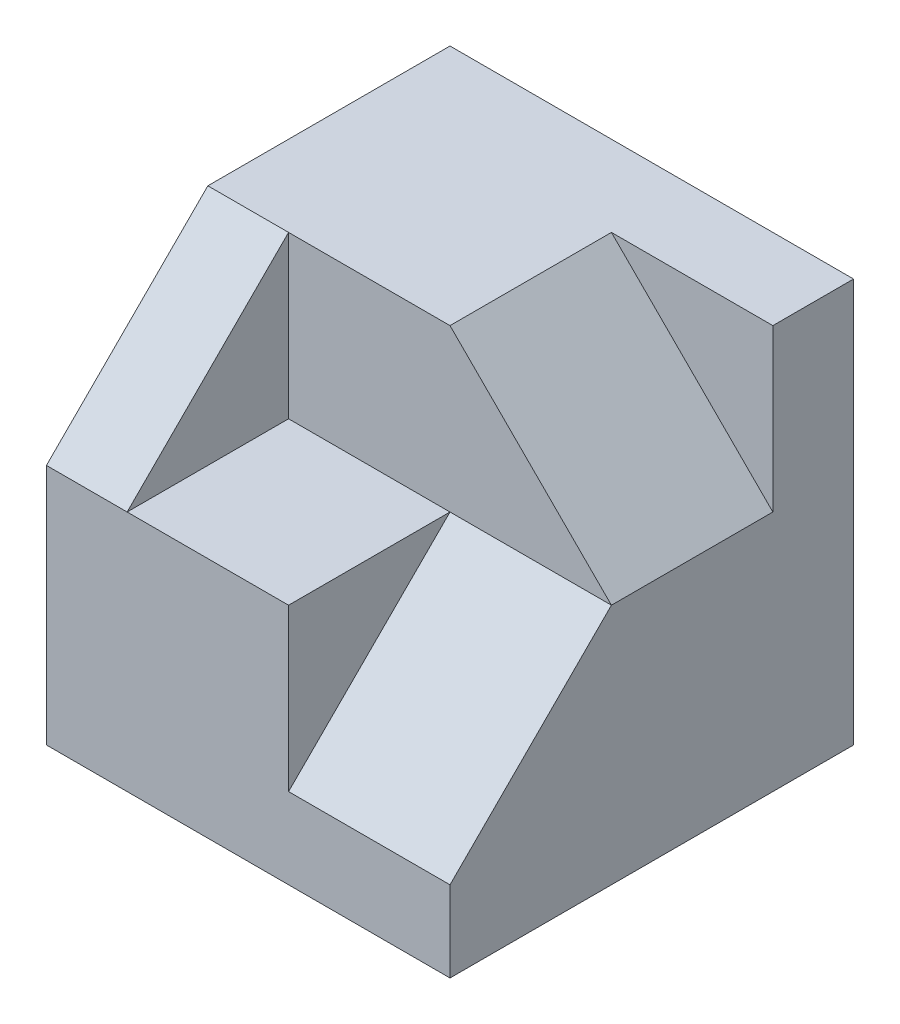
SolidWorks part; units mm, degrees
ref_plane "Front Plane" through (0, 0, 0) normal (0, 0, 1) x (1, 0, 0)
ref_plane "Top Plane" through (0, 0, 0) normal (0, 1, 0) x (1, 0, 0)
ref_plane "Right Plane" through (0, 0, 0) normal (1, 0, 0) x (0, 0, -1)
sketch "Sketch1" plane through (0, 0, 0) normal (0, 0, 1) x (1, 0, 0)
  line L1 (2.5, -2.5) -> (-2.5, -2.5)
  line L2 (2.5, -2.5) -> (2.5, 2.5)
  line L3 (2.5, 2.5) -> (-2.5, 2.5)
  line L4 (-2.5, -2.5) -> (-2.5, 2.5)
  line L5 (2.5, -2.5) -> (-2.5, 2.5) construction
  line L6 (2.5, 2.5) -> (-2.5, -2.5) construction
  point P0 (0, 0)
  dimension "D1" = 5
  dimension "D2" = 5
extrude "Boss-Extrude1" add sketch "Sketch1" along normal blind 5
sketch "Sketch2" plane through (2.5, 0, 0) normal (1, 0, 0) x (0, 0, -1)
  line L0 (-3, 2.5) -> (-5, 0.5)
  line L1 (-5, 2.5) -> (0, 2.5) construction
  line L2 (-5, -2.5) -> (-5, 2.5) construction
  line L3 (-5, 0.5) -> (-5, 2.5)
  line L4 (-5, 2.5) -> (-3, 2.5)
  dimension "D1" = 2
  dimension "D2" = 2
extrude "Cut-Extrude1" cut sketch "Sketch2" against normal blind 4
sketch "Sketch3" plane through (0, 2.5, 0) normal (0, 1, 0) x (1, 0, 0)
  line L0 (-1.5, -3) -> (-1.5, -5)
  line L1 (2.5, -5) -> (2.5, -3)
  line L2 (2.5, -3) -> (-1.5, -3)
  line L3 (-1.5, -5) -> (2.5, -5)
extrude "Cut-Extrude3" cut sketch "Sketch3" against normal blind 2
sketch "Sketch4" plane through (2.5, 0, 0) normal (1, 0, 0) x (0, 0, -1)
  line L0 (-3, 0.5) -> (-5, -1.5)
  line L1 (-5, -2.5) -> (-5, 0.5) construction
  line L2 (-5, -1.5) -> (-5, 0.5)
  line L3 (-5, 0.5) -> (-3, 0.5)
  dimension "D1" = 1
extrude "Cut-Extrude4" cut sketch "Sketch4" against normal blind 2
sketch "Sketch5" plane through (0, 0, 3) normal (0, 0, 1) x (1, 0, 0)
  line L0 (0.5, 2.5) -> (2.5, 0.5)
  line L1 (-1.5, 2.5) -> (2.5, 2.5) construction
  line L2 (2.5, 0.5) -> (2.5, 2.5)
  line L3 (2.5, 2.5) -> (0.5, 2.5)
extrude "Cut-Extrude5" cut sketch "Sketch5" against normal blind 2
sketch "Sketch6" plane through (-1.5, 0, 0) normal (1, 0, 0) x (0, 0, -1)
  line L0 (-3, 2.5) -> (-5, 0.5)
  line L1 (-5, 0.5) -> (-5, 2.5)
  line L2 (-5, 2.5) -> (-3, 2.5)
extrude "Cut-Extrude6" cut sketch "Sketch6" against normal through all
